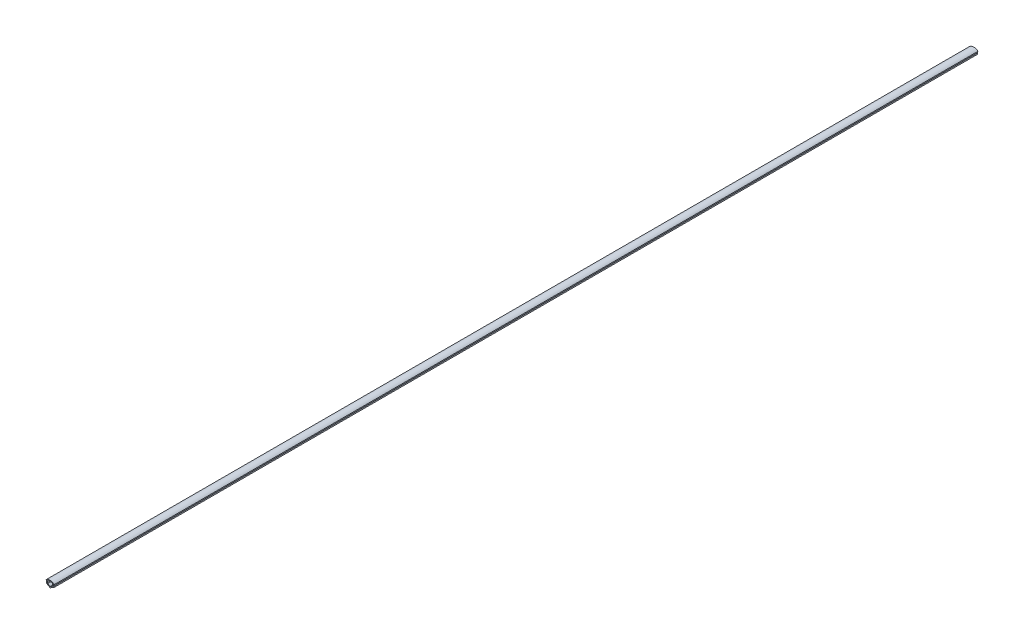
SolidWorks part; units mm, degrees
material "Пластик"
ref_plane "Спереди" through (0, 0, 0) normal (0, 0, 1) x (1, 0, 0)
ref_plane "Сверху" through (0, 0, 0) normal (0, 1, 0) x (1, 0, 0)
ref_plane "Справа" through (0, 0, 0) normal (1, 0, 0) x (0, 0, -1)
sketch "Эскиз1" plane through (0, 0, 0) normal (0, 0, 1) x (1, 0, 0)
  line L42 (0, 0) -> (-4.25, 2.4537)
  line L43 (-4.25, 2.4537) -> (-3.75, 3.3198)
  line L44 (-3.75, 3.3198) -> (-3.75, 5.3327)
  line L45 (-3.75, 5.3327) -> (-4.5346, 5.3327)
  line L46 (0, 0) -> (0, 7) construction
  line L47 (3.75, 5.3327) -> (4.5346, 5.3327)
  line L48 (3.75, 3.3198) -> (3.75, 5.3327)
  line L49 (4.25, 2.4537) -> (3.75, 3.3198)
  line L50 (0, 0) -> (4.25, 2.4537)
  line L51 (0, 1.1547) -> (-2.75, 2.7424)
  line L52 (-2.75, 2.7424) -> (-2.75, 5.3327)
  line L53 (2.75, 2.7424) -> (2.75, 5.3327)
  line L54 (0, 0) -> (4.25, 2.4537)
  line L55 (0, 1.1547) -> (2.75, 2.7424)
  arc A2 (-4.5346, 5.3327) -> (4.5346, 5.3327) centre (0, 0) cw
  arc A3 (-2.75, 5.3327) -> (2.75, 5.3327) centre (0, 0) cw
  dimension "D5" = 7
  dimension "D6" = 6
  dimension "D1" = 7.5
  dimension "D2" = 7
  dimension "D3" = 1
  dimension "D4" = 1
  dimension "D7" = 60
  dimension "D8" = 1
extrude "Бобышка-Вытянуть1" add sketch "Эскиз1" along normal blind 1000 contours L42 L46 L51 L52 A3 A2 L45 L44 L43 | L46 L50 L49 L48 L47 A2 A3 L53 L55
